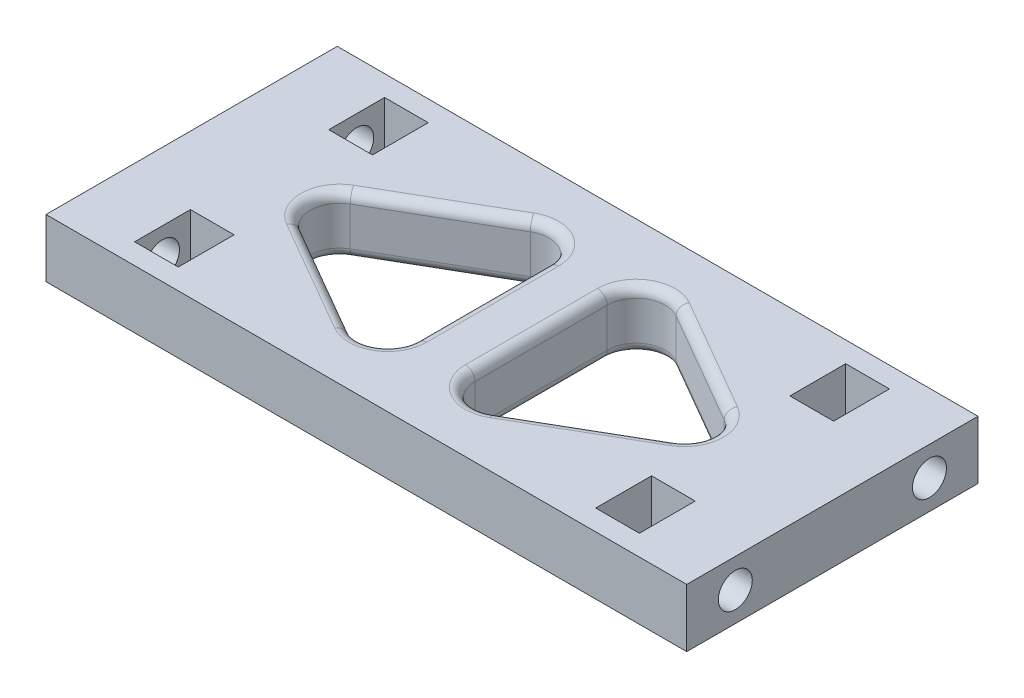
SolidWorks part; units mm, degrees
ref_plane "Front Plane" through (0, 0, 0) normal (0, 0, 1) x (1, 0, 0)
ref_plane "Top Plane" through (0, 0, 0) normal (0, 1, 0) x (1, 0, 0)
ref_plane "Right Plane" through (0, 0, 0) normal (1, 0, 0) x (0, 0, -1)
sketch "Sketch1" plane through (0, 0, 0) normal (1, 0, 0) x (0, 0, -1)
  line L1 (-15, 3) -> (15, 3)
  line L2 (-15, 3) -> (-15, -3)
  line L3 (-15, -3) -> (15, -3)
  line L4 (15, 3) -> (15, -3)
  line L5 (-15, 3) -> (15, -3) construction
  line L6 (-15, -3) -> (15, 3) construction
  point P0 (0, 0)
  dimension "D1" = 30
  dimension "D2" = 6
extrude "Boss-Extrude1" add sketch "Sketch1" along normal mid plane 66
sketch "Sketch2" plane through (33, 0, 0) normal (1, 0, 0) x (0, 0, -1)
  line L0 (0, 3) -> (0, -3) construction
  line L1 (15, 3) -> (-15, 3) construction
  line L2 (-15, -3) -> (15, -3) construction
  line L3 (-15, 0) -> (15, 0) construction
  line L4 (-15, 3) -> (-15, -3) construction
  line L5 (15, -3) -> (15, 3) construction
  circle A0 centre (-10, 0) radius 1.75
  circle A1 centre (10, 0) radius 1.75
  dimension "D2" = 3.5
  dimension "D1" = 20
extrude "Cut-Extrude1" cut sketch "Sketch2" against normal blind 7
ref_plane "Plane1" through (26, 0, 0) normal (1, 0, 0) x (0, 0, -1)
sketch "Sketch3" plane through (26, 0, 0) normal (1, 0, 0) x (0, 0, -1)
  line L0 (-12.875, 1.6599) -> (-12.875, 3)
  line L1 (-12.875, -1.6599) -> (-10, -3.3198)
  line L2 (-10, -3.3198) -> (-7.125, -1.6599)
  line L3 (-7.125, -1.6599) -> (-7.125, 1.6599)
  line L4 (-7.125, 1.6599) -> (-10, 3.3198)
  line L5 (-10, 3.3198) -> (-12.875, 1.6599)
  line L6 (-12.875, 1.6599) -> (-12.875, -1.6599)
  line L7 (15, 3) -> (-15, 3) construction
  line L8 (-12.875, 3) -> (-7.125, 3)
  line L9 (-7.125, 3) -> (-7.125, 1.6599)
  line L10 (0, 3) -> (0, -3) construction
  line L11 (-15, -3) -> (15, -3) construction
  line L12 (7.125, 3) -> (7.125, 1.6599)
  line L13 (12.875, 3) -> (7.125, 3)
  line L14 (12.875, 1.6599) -> (12.875, 3)
  line L15 (7.125, -1.6599) -> (7.125, 1.6599)
  line L16 (10, -3.3198) -> (7.125, -1.6599)
  line L17 (12.875, -1.6599) -> (10, -3.3198)
  line L18 (12.875, 1.6599) -> (12.875, -1.6599)
  circle A0 centre (-10, 0) radius 2.875 construction
  dimension "D1" = 5.75
extrude "Cut-Extrude2" cut sketch "Sketch3" against normal blind 4.5 contours L5 L6 L1 L2 L3 L4 | L9 L8 L0 L5 L4 | L18 L14 L13 L12 L15 L16 L17 | L9 L8 L4
mirror "Mirror1" about plane through (0, 0, 0) normal (1, 0, 0) of "Cut-Extrude2", "Cut-Extrude1"
sketch "Sketch4" plane through (0, 3, 0) normal (0, 1, 0) x (1, 0, 0)
  line L0 (-33, 0) -> (33, 0) construction
  line L1 (-33, 15) -> (-33, -15) construction
  line L2 (33, 15) -> (33, -15) construction
  line L3 (-23.75, 7.125) -> (-23.75, -7.125) construction
  line L4 (-21.5, 7.125) -> (-26, 7.125) construction
  line L6 (0, 15) -> (0, -15) construction
  line L7 (33, 15) -> (-33, 15) construction
  line L8 (33, -15) -> (-33, -15) construction
  line L9 (-3, 15) -> (-3, -15)
  line L10 (3, 15) -> (3, -15)
  line L11 (-33, 12) -> (33, 12) construction
  line L12 (-23.75, 0) -> (-3, 12)
  line L13 (-23.75, 0) -> (-3, -12)
  line L14 (23.75, 0) -> (3, -12)
  line L15 (23.75, 0) -> (3, 12)
  line L16 (-21.5, -7.125) -> (-26, -7.125) construction
  dimension "D3" = 3
  dimension "D1" = 3
  dimension "D2" = 3
extrude "Cut-Extrude3" cut sketch "Sketch4" against normal through all contours L12 L13 L9 | L14 L15 L10
fillet "Fillet1" radius 3 6 edges at (23.75, 0, 0) (3, 0, 12) (3, 0, -12) (-3, 0, 12) (-23.75, 0, 0) (-3, 0, -12)
fillet "Fillet2" radius 1 24 edges at (20.7575, 3, 0) (13.3806, 3, 5.9967) (4.5009, 3, 9.3981) (3, 3, 0) (4.5009, 3, -9.3981) (20.7575, -3, 0) (13.3806, -3, 5.9967) (4.5009, -3, 9.3981) (3, -3, 0) (4.5009, -3, -9.3981) (-20.7575, -3, 0) (-13.3806, -3, 5.9967) (-4.5009, -3, 9.3981) (-3, -3, 0) (-4.5009, -3, -9.3981) (-20.7575, 3, 0) (-13.3806, 3, 5.9967) (-4.5009, 3, 9.3981) (-3, 3, 0) (-4.5009, 3, -9.3981) (13.3806, 3, -5.9967) (13.3806, -3, -5.9967) (-13.3806, -3, -5.9967) (-13.3806, 3, -5.9967)
fillet "Fillet3" radius 0.5 8 edges at (-23.75, -3, -10.5538) (-23.75, -3, -9.4462) (-23.75, -3, 9.4462) (-23.75, -3, 10.5538) (23.75, -3, -9.4462) (23.75, -3, -10.5538) (23.75, -3, 10.5538) (23.75, -3, 9.4462)
